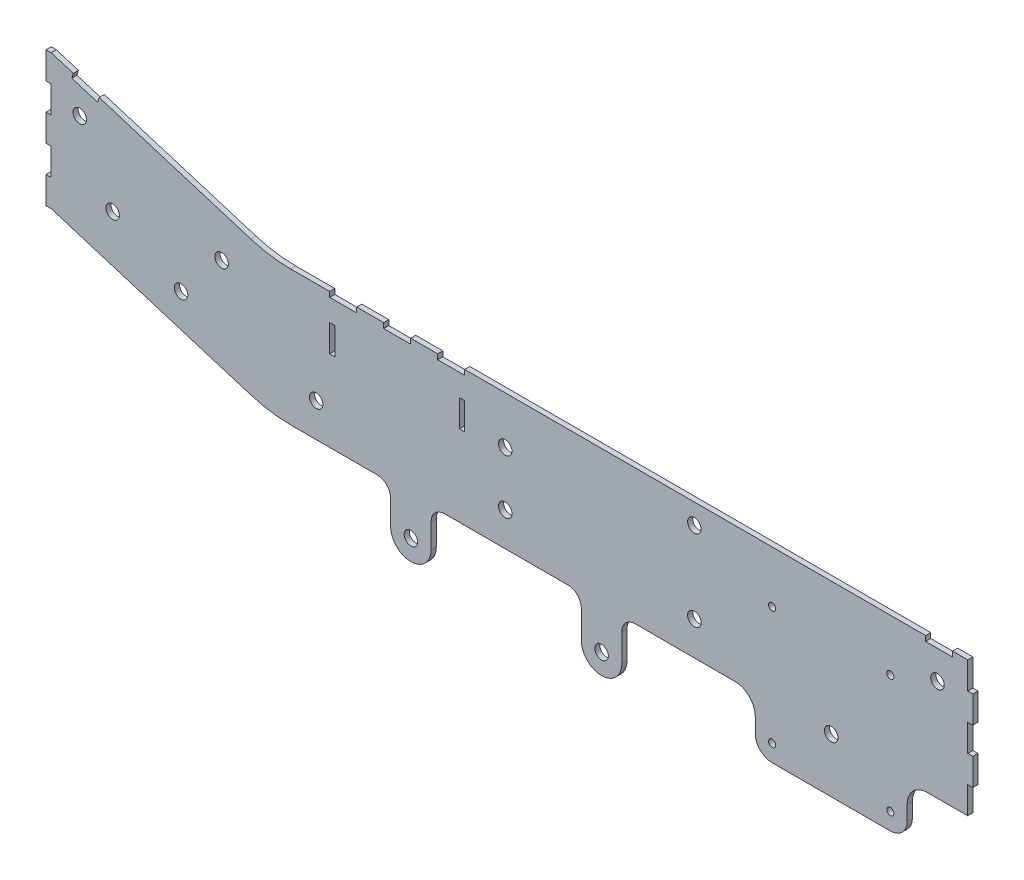
SolidWorks part; units mm, degrees
material "1060 Alloy"
ref_plane "Front Plane" through (0, 0, 0) normal (0, 0, 1) x (1, 0, 0)
ref_plane "Top Plane" through (0, 0, 0) normal (0, 1, 0) x (1, 0, 0)
ref_plane "Right Plane" through (0, 0, 0) normal (1, 0, 0) x (0, 0, -1)
sketch "Sketch2" plane through (0, 0, 0) normal (0, 0, 1) x (1, 0, 0)
  line L41 (-214.6997, -160.1998) -> (-26.8739, -218.0697)
  line L42 (10.5206, -223.6998) -> (91.8093, -223.6998)
  line L43 (104.5093, -236.3998) -> (104.5093, -259.4448)
  line L44 (142.6093, -259.4448) -> (142.6093, -236.3998)
  line L45 (155.3093, -223.6998) -> (271.0993, -223.6998)
  line L46 (283.7993, -236.3998) -> (283.7993, -262.6248)
  line L47 (321.8993, -262.6248) -> (321.8993, -236.3998)
  line L48 (334.5993, -223.6998) -> (476.2017, -223.6998)
  line L49 (561.2969, -223.6998) -> (656.7743, -223.6998)
  line L50 (656.7743, -223.6998) -> (656.7743, -198.2998)
  line L51 (656.7743, -198.2998) -> (651.9483, -198.2998)
  line L52 (651.9483, -198.2998) -> (651.9483, -172.8998)
  line L53 (651.9483, -172.8998) -> (656.7743, -172.8998)
  line L54 (656.7743, -172.8998) -> (656.7743, -147.4998)
  line L55 (656.7743, -147.4998) -> (651.9483, -147.4998)
  line L56 (651.9483, -147.4998) -> (651.9483, -122.0998)
  line L57 (651.9483, -122.0998) -> (656.7743, -122.0998)
  line L58 (656.7743, -122.0998) -> (656.7743, -96.6998)
  line L59 (656.7743, -96.6998) -> (174.1743, -96.6998)
  line L60 (174.1743, -96.6998) -> (174.1743, -101.5258)
  line L61 (174.1743, -101.5258) -> (148.7743, -101.5258)
  line L62 (148.7743, -101.5258) -> (148.7743, -96.6998)
  line L63 (148.7743, -96.6998) -> (123.3743, -96.6998)
  line L64 (123.3743, -96.6998) -> (123.3743, -101.5258)
  line L65 (123.3743, -101.5258) -> (97.9743, -101.5258)
  line L66 (97.9743, -101.5258) -> (97.9743, -96.6998)
  line L67 (97.9743, -96.6998) -> (72.5743, -96.6998)
  line L68 (72.5743, -96.6998) -> (72.5743, -101.5258)
  line L69 (72.5743, -101.5258) -> (47.1743, -101.5258)
  line L70 (47.1743, -101.5258) -> (47.1743, -96.6998)
  line L71 (47.1743, -96.6998) -> (10.5206, -96.6998)
  line L72 (-214.6997, -160.1998) -> (-26.8739, -218.0697)
  line L73 (-219.5257, -33.1998) -> (-219.5257, -58.5998)
  line L74 (-219.5257, -58.5998) -> (-214.6997, -58.5998)
  line L75 (-214.6997, -58.5998) -> (-214.6997, -83.9998)
  line L76 (-214.6997, -83.9998) -> (-219.5257, -83.9998)
  line L77 (-219.5257, -83.9998) -> (-219.5257, -109.3998)
  line L78 (-219.5257, -109.3998) -> (-214.6997, -109.3998)
  line L79 (-214.6997, -109.3998) -> (-214.6997, -134.7998)
  line L80 (-214.6997, -134.7998) -> (-219.5257, -134.7998)
  line L81 (-219.5257, -134.7998) -> (-219.5257, -160.1998)
  line L82 (-26.8739, -91.0697) -> (-169.5568, -47.1085)
  line L83 (10.5206, -223.6998) -> (91.8093, -223.6998)
  line L84 (104.5093, -236.3998) -> (104.5093, -259.4448)
  line L85 (142.6093, -259.4448) -> (142.6093, -236.3998)
  line L86 (155.3093, -223.6998) -> (271.0993, -223.6998)
  line L87 (283.7993, -236.3998) -> (283.7993, -262.6248)
  line L88 (321.8993, -262.6248) -> (321.8993, -236.3998)
  line L89 (334.5993, -223.6998) -> (476.2017, -223.6998)
  line L90 (561.2969, -223.6998) -> (656.7743, -223.6998)
  line L91 (656.7743, -223.6998) -> (656.7743, -198.2998)
  line L92 (656.7743, -198.2998) -> (651.9483, -198.2998)
  line L93 (651.9483, -198.2998) -> (651.9483, -172.8998)
  line L94 (651.9483, -172.8998) -> (656.7743, -172.8998)
  line L95 (656.7743, -172.8998) -> (656.7743, -147.4998)
  line L96 (656.7743, -147.4998) -> (651.9483, -147.4998)
  line L97 (651.9483, -147.4998) -> (651.9483, -122.0998)
  line L98 (651.9483, -122.0998) -> (656.7743, -122.0998)
  line L99 (656.7743, -122.0998) -> (656.7743, -96.6998)
  line L100 (656.7743, -96.6998) -> (174.1743, -96.6998)
  line L101 (174.1743, -96.6998) -> (174.1743, -101.5258)
  line L102 (174.1743, -101.5258) -> (148.7743, -101.5258)
  line L103 (148.7743, -101.5258) -> (148.7743, -96.6998)
  line L104 (148.7743, -96.6998) -> (123.3743, -96.6998)
  line L105 (123.3743, -96.6998) -> (123.3743, -101.5258)
  line L106 (123.3743, -101.5258) -> (97.9743, -101.5258)
  line L107 (97.9743, -101.5258) -> (97.9743, -96.6998)
  line L108 (97.9743, -96.6998) -> (72.5743, -96.6998)
  line L109 (72.5743, -96.6998) -> (72.5743, -101.5258)
  line L110 (72.5743, -101.5258) -> (47.1743, -101.5258)
  line L111 (47.1743, -101.5258) -> (47.1743, -96.6998)
  line L112 (47.1743, -96.6998) -> (10.5206, -96.6998)
  line L113 (-26.8739, -91.0697) -> (-169.5568, -47.1085)
  line L114 (-219.5257, -33.1998) -> (-219.5257, -58.5998)
  line L115 (-219.5257, -58.5998) -> (-214.6997, -58.5998)
  line L116 (-214.6997, -58.5998) -> (-214.6997, -83.9998)
  line L117 (-214.6997, -83.9998) -> (-219.5257, -83.9998)
  line L118 (-219.5257, -83.9998) -> (-219.5257, -109.3998)
  line L119 (-219.5257, -109.3998) -> (-214.6997, -109.3998)
  line L120 (-214.6997, -109.3998) -> (-214.6997, -134.7998)
  line L121 (-214.6997, -134.7998) -> (-219.5257, -134.7998)
  line L122 (-219.5257, -134.7998) -> (-219.5257, -160.1998)
  line L176 (-195.2517, -44.2417) -> (-193.8307, -39.6296)
  line L177 (-195.2517, -44.2417) -> (-193.8307, -39.6296)
  line L178 (-193.8307, -39.6296) -> (-214.6997, -33.1998)
  line L179 (-193.8307, -39.6296) -> (-214.6997, -33.1998)
  line L180 (-169.5568, -47.1085) -> (-170.9777, -51.7206)
  line L181 (-169.5568, -47.1085) -> (-170.9777, -51.7206)
  line L182 (-170.9777, -51.7206) -> (-195.2517, -44.2417)
  line L183 (-170.9777, -51.7206) -> (-195.2517, -44.2417)
  line L412 (-214.6997, -33.1998) -> (-219.5257, -33.1998)
  line L413 (-214.6997, -33.1998) -> (-219.5257, -33.1998)
  line L414 (-219.5257, -160.1998) -> (-214.6997, -160.1998)
  line L415 (-219.5257, -160.1998) -> (-214.6997, -160.1998)
  arc A11 (-26.8739, -218.0697) -> (10.5206, -223.6998) centre (10.5206, -96.6998) ccw
  arc A12 (104.5093, -236.3998) -> (91.8093, -223.6998) centre (91.8093, -236.3998) ccw
  arc A13 (104.5093, -259.4448) -> (142.6093, -259.4448) centre (123.5593, -259.4448) ccw
  arc A14 (155.3093, -223.6998) -> (142.6093, -236.3998) centre (155.3093, -236.3998) ccw
  arc A15 (283.7993, -236.3998) -> (271.0993, -223.6998) centre (271.0993, -236.3998) ccw
  arc A16 (283.7993, -262.6248) -> (321.8993, -262.6248) centre (302.8493, -262.6248) ccw
  arc A17 (334.5993, -223.6998) -> (321.8993, -236.3998) centre (334.5993, -236.3998) ccw
  arc A18 (486.8386, -229.461) -> (476.2017, -223.6998) centre (476.2017, -236.3998) ccw
  arc A19 (486.8386, -229.461) -> (550.66, -229.461) centre (518.7493, -208.6448) ccw
  arc A20 (561.2969, -223.6998) -> (550.66, -229.461) centre (561.2969, -236.3998) ccw
  arc A21 (-26.8739, -218.0697) -> (10.5206, -223.6998) centre (10.5206, -96.6998) ccw
  arc A22 (-26.8739, -91.0697) -> (10.5206, -96.6998) centre (10.5206, 30.3002) ccw
  arc A23 (104.5093, -236.3998) -> (91.8093, -223.6998) centre (91.8093, -236.3998) ccw
  arc A24 (104.5093, -259.4448) -> (142.6093, -259.4448) centre (123.5593, -259.4448) ccw
  arc A25 (155.3093, -223.6998) -> (142.6093, -236.3998) centre (155.3093, -236.3998) ccw
  arc A26 (283.7993, -236.3998) -> (271.0993, -223.6998) centre (271.0993, -236.3998) ccw
  arc A27 (283.7993, -262.6248) -> (321.8993, -262.6248) centre (302.8493, -262.6248) ccw
  arc A28 (334.5993, -223.6998) -> (321.8993, -236.3998) centre (334.5993, -236.3998) ccw
  arc A29 (486.8386, -229.461) -> (476.2017, -223.6998) centre (476.2017, -236.3998) ccw
  arc A30 (486.8386, -229.461) -> (550.66, -229.461) centre (518.7493, -208.6448) ccw
  arc A31 (561.2969, -223.6998) -> (550.66, -229.461) centre (561.2969, -236.3998) ccw
  arc A32 (-26.8739, -91.0697) -> (10.5206, -96.6998) centre (10.5206, 30.3002) ccw
  circle A56 centre (390.0743, -191.9498) radius 6.35
  circle A57 centre (390.0743, -191.9498) radius 6.35
  circle A58 centre (390.0743, -115.7498) radius 6.35
  circle A59 centre (390.0743, -115.7498) radius 6.35
  circle A60 centre (518.7493, -221.3448) radius 6.35
  circle A61 centre (518.7493, -221.3448) radius 6.35
  circle A62 centre (618.6743, -128.4498) radius 6.35
  circle A63 centre (618.6743, -128.4498) radius 6.35
  circle A64 centre (302.8493, -262.6248) radius 6.35
  circle A65 centre (302.8493, -262.6248) radius 6.35
  circle A66 centre (212.2743, -191.9498) radius 6.35
  circle A67 centre (212.2743, -191.9498) radius 6.35
  circle A68 centre (212.2743, -141.1498) radius 6.35
  circle A69 centre (212.2743, -141.1498) radius 6.35
  circle A70 centre (123.5593, -259.4448) radius 6.35
  circle A71 centre (123.5593, -259.4448) radius 6.35
  circle A72 centre (34.4743, -191.9498) radius 6.35
  circle A73 centre (34.4743, -191.9498) radius 6.35
  circle A74 centre (-92.5257, -166.5498) radius 6.35
  circle A75 centre (-92.5257, -166.5498) radius 6.35
  circle A76 centre (-156.8507, -133.7248) radius 6.35
  circle A77 centre (-156.8507, -133.7248) radius 6.35
  circle A78 centre (-54.4257, -122.0998) radius 6.35
  circle A79 centre (-54.4257, -122.0998) radius 6.35
  circle A80 centre (-187.7757, -71.2998) radius 6.35
  circle A81 centre (-187.7757, -71.2998) radius 6.35
  dimension "D1" = 0
  dimension "D2" = 0
  dimension "D3" = 0
  dimension "D4" = 0
  dimension "D5" = 0
  dimension "D6" = 0
  dimension "D7" = 0
  dimension "D8" = 0
  dimension "D9" = 0
  dimension "D10" = 0
  dimension "D11" = 0
  dimension "D12" = 0
  dimension "D13" = 0
  dimension "D14" = 0
extrude "base" add sketch "Sketch2" along normal blind 4.826
sketch "Sketch3" plane through (0, 0, 4.826) normal (0, 0, 1) x (1, 0, 0)
  line L0 (47.1743, -101.5258) -> (47.1743, -96.6998) construction
  line L1 (169.3483, -122.0998) -> (174.1743, -122.0998)
  line L2 (169.3483, -122.0998) -> (169.3483, -147.4998)
  line L3 (169.3483, -147.4998) -> (174.1743, -147.4998)
  line L4 (174.1743, -122.0998) -> (174.1743, -147.4998)
  line L5 (47.1743, -122.0998) -> (52.0003, -122.0998)
  line L6 (47.1743, -122.0998) -> (47.1743, -147.4998)
  line L7 (47.1743, -147.4998) -> (52.0003, -147.4998)
  line L8 (52.0003, -122.0998) -> (52.0003, -147.4998)
  line L9 (174.1743, -96.6998) -> (174.1743, -101.5258) construction
  line L10 (97.9743, -96.6998) -> (72.5743, -96.6998) construction
  dimension "D1" = 4.826
  dimension "D2" = 25.4
  dimension "D3" = 25.4
extrude "center support vertical holes" cut sketch "Sketch3" against normal through all
sketch "Sketch4" plane through (656.7743, 0, 0) normal (1, 0, 0) x (0, 0, -1)
  line L0 (0, -122.0998) -> (0, -96.6998) construction
  line L1 (0, -96.6998) -> (-4.826, -96.6998) construction
  line L2 (-4.826, -96.6998) -> (-4.826, -122.0998) construction
  line L3 (-4.826, -122.0998) -> (0, -122.0998) construction
  line L4 (0, -172.8998) -> (0, -147.4998) construction
  line L5 (0, -147.4998) -> (-4.826, -147.4998) construction
  line L6 (-4.826, -147.4998) -> (-4.826, -172.8998) construction
  line L7 (-4.826, -172.8998) -> (0, -172.8998) construction
  line L8 (0, -223.6998) -> (0, -198.2998) construction
  line L9 (0, -198.2998) -> (-4.826, -198.2998) construction
  line L10 (-4.826, -198.2998) -> (-4.826, -223.6998) construction
  line L11 (-4.826, -223.6998) -> (0, -223.6998) construction
  line L12 (0, -122.0998) -> (0, -96.6998)
  line L13 (0, -96.6998) -> (-4.826, -96.6998)
  line L14 (-4.826, -96.6998) -> (-4.826, -122.0998)
  line L15 (-4.826, -122.0998) -> (0, -122.0998)
  line L16 (0, -172.8998) -> (0, -147.4998)
  line L17 (0, -147.4998) -> (-4.826, -147.4998)
  line L18 (-4.826, -147.4998) -> (-4.826, -172.8998)
  line L19 (-4.826, -172.8998) -> (0, -172.8998)
  line L20 (0, -223.6998) -> (0, -198.2998)
  line L21 (0, -198.2998) -> (-4.826, -198.2998)
  line L22 (-4.826, -198.2998) -> (-4.826, -223.6998)
  line L23 (-4.826, -223.6998) -> (0, -223.6998)
extrude "Cut-Extrude2" cut sketch "Sketch4" against normal blind 9.652
sketch "Sketch5" plane through (0, 0, 0) normal (0, 0, 1) x (1, 0, 0)
  line L0 (463.2122, -272.4369) -> (574.3372, -272.4369)
  line L1 (447.3372, -256.5619) -> (447.3372, -242.7498)
  line L3 (590.2122, -256.5619) -> (590.2122, -242.7498)
  line L43 (647.1223, -198.2998) -> (651.9483, -198.2998)
  line L44 (651.9483, -198.2998) -> (651.9483, -172.8998)
  line L45 (651.9483, -172.8998) -> (647.1223, -172.8998)
  line L46 (647.1223, -172.8998) -> (647.1223, -147.4998)
  line L47 (647.1223, -147.4998) -> (651.9483, -147.4998)
  line L48 (651.9483, -147.4998) -> (651.9483, -122.0998)
  line L49 (651.9483, -122.0998) -> (647.1223, -122.0998)
  line L50 (647.1223, -122.0998) -> (647.1223, -96.6998)
  line L51 (647.1223, -96.6998) -> (174.1743, -96.6998)
  line L52 (174.1743, -96.6998) -> (174.1743, -101.5258)
  line L53 (174.1743, -101.5258) -> (148.7743, -101.5258)
  line L54 (148.7743, -101.5258) -> (148.7743, -96.6998)
  line L55 (148.7743, -96.6998) -> (123.3743, -96.6998)
  line L56 (123.3743, -96.6998) -> (123.3743, -101.5258)
  line L57 (123.3743, -101.5258) -> (97.9743, -101.5258)
  line L58 (97.9743, -101.5258) -> (97.9743, -96.6998)
  line L59 (97.9743, -96.6998) -> (72.5743, -96.6998)
  line L60 (72.5743, -96.6998) -> (72.5743, -101.5258)
  line L61 (72.5743, -101.5258) -> (47.1743, -101.5258)
  line L62 (47.1743, -101.5258) -> (47.1743, -96.6998)
  line L63 (47.1743, -96.6998) -> (10.5206, -96.6998)
  line L64 (-26.8739, -91.0697) -> (-169.5568, -47.1085)
  line L65 (-214.6997, -33.1998) -> (-219.5257, -33.1998)
  line L66 (-219.5257, -33.1998) -> (-219.5257, -58.5998)
  line L67 (-219.5257, -58.5998) -> (-214.6997, -58.5998)
  line L68 (-214.6997, -58.5998) -> (-214.6997, -83.9998)
  line L69 (-214.6997, -83.9998) -> (-219.5257, -83.9998)
  line L70 (-219.5257, -83.9998) -> (-219.5257, -109.3998)
  line L71 (-219.5257, -109.3998) -> (-214.6997, -109.3998)
  line L72 (-214.6997, -109.3998) -> (-214.6997, -134.7998)
  line L73 (-214.6997, -134.7998) -> (-219.5257, -134.7998)
  line L74 (-219.5257, -134.7998) -> (-219.5257, -160.1998)
  line L75 (-219.5257, -160.1998) -> (-214.6997, -160.1998)
  line L76 (-214.6997, -160.1998) -> (-26.8739, -218.0697)
  line L77 (10.5206, -223.6998) -> (91.8093, -223.6998)
  line L78 (104.5093, -236.3998) -> (104.5093, -259.4448)
  line L79 (142.6093, -259.4448) -> (142.6093, -236.3998)
  line L80 (155.3093, -223.6998) -> (271.0993, -223.6998)
  line L81 (283.7993, -236.3998) -> (283.7993, -262.6248)
  line L82 (321.8993, -262.6248) -> (321.8993, -236.3998)
  line L83 (334.5993, -223.6998) -> (476.2017, -223.6998)
  line L84 (561.2969, -223.6998) -> (647.1223, -223.6998)
  line L85 (647.1223, -223.6998) -> (647.1223, -198.2998)
  line L86 (647.1223, -198.2998) -> (651.9483, -198.2998)
  line L87 (651.9483, -198.2998) -> (651.9483, -172.8998)
  line L88 (651.9483, -172.8998) -> (647.1223, -172.8998)
  line L89 (647.1223, -172.8998) -> (647.1223, -147.4998)
  line L90 (647.1223, -147.4998) -> (651.9483, -147.4998)
  line L91 (651.9483, -147.4998) -> (651.9483, -122.0998)
  line L92 (651.9483, -122.0998) -> (647.1223, -122.0998)
  line L93 (647.1223, -122.0998) -> (647.1223, -96.6998)
  line L94 (647.1223, -96.6998) -> (174.1743, -96.6998)
  line L95 (174.1743, -96.6998) -> (174.1743, -101.5258)
  line L96 (174.1743, -101.5258) -> (148.7743, -101.5258)
  line L97 (148.7743, -101.5258) -> (148.7743, -96.6998)
  line L98 (148.7743, -96.6998) -> (123.3743, -96.6998)
  line L99 (123.3743, -96.6998) -> (123.3743, -101.5258)
  line L100 (123.3743, -101.5258) -> (97.9743, -101.5258)
  line L101 (97.9743, -101.5258) -> (97.9743, -96.6998)
  line L102 (97.9743, -96.6998) -> (72.5743, -96.6998)
  line L103 (72.5743, -96.6998) -> (72.5743, -101.5258)
  line L104 (72.5743, -101.5258) -> (47.1743, -101.5258)
  line L105 (47.1743, -101.5258) -> (47.1743, -96.6998)
  line L106 (47.1743, -96.6998) -> (10.5206, -96.6998)
  line L107 (-26.8739, -91.0697) -> (-169.5568, -47.1085)
  line L108 (-214.6997, -33.1998) -> (-219.5257, -33.1998)
  line L109 (-219.5257, -33.1998) -> (-219.5257, -58.5998)
  line L110 (-219.5257, -58.5998) -> (-214.6997, -58.5998)
  line L111 (-214.6997, -58.5998) -> (-214.6997, -83.9998)
  line L112 (-214.6997, -83.9998) -> (-219.5257, -83.9998)
  line L113 (-219.5257, -83.9998) -> (-219.5257, -109.3998)
  line L114 (-219.5257, -109.3998) -> (-214.6997, -109.3998)
  line L115 (-214.6997, -109.3998) -> (-214.6997, -134.7998)
  line L116 (-214.6997, -134.7998) -> (-219.5257, -134.7998)
  line L117 (-219.5257, -134.7998) -> (-219.5257, -160.1998)
  line L118 (-219.5257, -160.1998) -> (-214.6997, -160.1998)
  line L119 (-214.6997, -160.1998) -> (-26.8739, -218.0697)
  line L120 (10.5206, -223.6998) -> (91.8093, -223.6998)
  line L121 (104.5093, -236.3998) -> (104.5093, -259.4448)
  line L122 (142.6093, -259.4448) -> (142.6093, -236.3998)
  line L123 (155.3093, -223.6998) -> (271.0993, -223.6998)
  line L124 (283.7993, -236.3998) -> (283.7993, -262.6248)
  line L125 (321.8993, -262.6248) -> (321.8993, -236.3998)
  line L126 (334.5993, -223.6998) -> (476.2017, -223.6998)
  line L127 (561.2969, -223.6998) -> (647.1223, -223.6998)
  line L128 (647.1223, -223.6998) -> (647.1223, -198.2998)
  line L136 (-169.5568, -47.1085) -> (-170.9777, -51.7206)
  line L137 (-169.5568, -47.1085) -> (-170.9777, -51.7206)
  line L138 (-170.9777, -51.7206) -> (-195.2517, -44.2417)
  line L139 (-170.9777, -51.7206) -> (-195.2517, -44.2417)
  line L140 (-195.2517, -44.2417) -> (-193.8307, -39.6296)
  line L141 (-195.2517, -44.2417) -> (-193.8307, -39.6296)
  line L142 (-193.8307, -39.6296) -> (-214.6997, -33.1998)
  line L143 (-193.8307, -39.6296) -> (-214.6997, -33.1998)
  circle A0 centre (574.3372, -256.5619) radius 3.3528 construction
  circle A1 centre (463.2122, -256.5619) radius 3.3528 construction
  circle A2 centre (463.2122, -145.4369) radius 3.3528 construction
  circle A3 centre (574.3372, -145.4369) radius 3.2512 construction
  circle A4 centre (574.3372, -256.5619) radius 3.3528
  circle A5 centre (463.2122, -256.5619) radius 3.3528
  circle A6 centre (463.2122, -145.4369) radius 3.3528
  circle A7 centre (574.3372, -145.4369) radius 3.2512
  arc A8 (447.3372, -256.5619) -> (463.2122, -272.4369) centre (463.2122, -256.5619) ccw
  arc A9 (574.3372, -272.4369) -> (590.2122, -256.5619) centre (574.3372, -256.5619) ccw
  arc A10 (447.3372, -242.7498) -> (428.2872, -223.6998) centre (428.2872, -242.7498) ccw
  arc A11 (609.2622, -223.6998) -> (590.2122, -242.7498) centre (609.2622, -242.7498) ccw
  arc A21 (-26.8739, -91.0697) -> (10.5206, -96.6998) centre (10.5206, 30.3002) ccw
  arc A22 (-26.8739, -218.0697) -> (10.5206, -223.6998) centre (10.5206, -96.6998) ccw
  arc A23 (104.5093, -236.3998) -> (91.8093, -223.6998) centre (91.8093, -236.3998) ccw
  arc A24 (104.5093, -259.4448) -> (142.6093, -259.4448) centre (123.5593, -259.4448) ccw
  arc A25 (155.3093, -223.6998) -> (142.6093, -236.3998) centre (155.3093, -236.3998) ccw
  arc A26 (283.7993, -236.3998) -> (271.0993, -223.6998) centre (271.0993, -236.3998) ccw
  arc A27 (283.7993, -262.6248) -> (321.8993, -262.6248) centre (302.8493, -262.6248) ccw
  arc A28 (334.5993, -223.6998) -> (321.8993, -236.3998) centre (334.5993, -236.3998) ccw
  arc A29 (486.8386, -229.461) -> (476.2017, -223.6998) centre (476.2017, -236.3998) ccw
  arc A30 (486.8386, -229.461) -> (550.66, -229.461) centre (518.7493, -208.6448) ccw
  arc A31 (561.2969, -223.6998) -> (550.66, -229.461) centre (561.2969, -236.3998) ccw
  arc A32 (-26.8739, -91.0697) -> (10.5206, -96.6998) centre (10.5206, 30.3002) ccw
  arc A33 (-26.8739, -218.0697) -> (10.5206, -223.6998) centre (10.5206, -96.6998) ccw
  arc A34 (104.5093, -236.3998) -> (91.8093, -223.6998) centre (91.8093, -236.3998) ccw
  arc A35 (104.5093, -259.4448) -> (142.6093, -259.4448) centre (123.5593, -259.4448) ccw
  arc A36 (155.3093, -223.6998) -> (142.6093, -236.3998) centre (155.3093, -236.3998) ccw
  arc A37 (283.7993, -236.3998) -> (271.0993, -223.6998) centre (271.0993, -236.3998) ccw
  arc A38 (283.7993, -262.6248) -> (321.8993, -262.6248) centre (302.8493, -262.6248) ccw
  arc A39 (334.5993, -223.6998) -> (321.8993, -236.3998) centre (334.5993, -236.3998) ccw
  arc A40 (486.8386, -229.461) -> (476.2017, -223.6998) centre (476.2017, -236.3998) ccw
  arc A41 (486.8386, -229.461) -> (550.66, -229.461) centre (518.7493, -208.6448) ccw
  arc A42 (561.2969, -223.6998) -> (550.66, -229.461) centre (561.2969, -236.3998) ccw
  arc M56 (455.2747, -263.7056) -> (456.0685, -264.4994) centre (456.0685, -263.7056) ccw
  line M57 (456.0685, -264.4994) -> (581.481, -264.4994)
  arc M58 (581.481, -264.4994) -> (582.2747, -263.7056) centre (581.481, -263.7056) ccw
  line M59 (582.2747, -263.7056) -> (582.2747, -138.2931)
  line M63 (455.2747, -138.2931) -> (455.2747, -263.7056)
  circle M64 centre (480.5665, -220.0494) radius 5.5626
  circle M68 centre (463.2122, -256.5619) radius 3.3528
  circle M70 centre (574.3372, -256.5619) radius 3.3528
  circle M74 centre (556.9829, -220.0494) radius 5.5626
  dimension "D2" = 31.75
  dimension "D3" = 19.05
  dimension "D1" = 0
extrude "Boss-Extrude1" add sketch "Sketch5" along normal through all contours A11 L127 L126 A10 L1 A8 L0 A9 L3 M59 M58 M57 M56 M63 | L127 A42 A41 A40 L126 M74 M64 M63 M56 M57 M58 M59 M70 M68 | A40 M64 | A42 M74
sketch "Sketch6" plane through (0, 0, 4.826) normal (0, 0, 1) x (1, 0, 0)
  circle A0 centre (463.1868, -145.4369) radius 3.3528 construction
  circle A2 centre (463.1868, -145.4369) radius 3.3528
  circle A3 centre (574.3118, -145.4369) radius 3.3528 construction
  circle A4 centre (574.3118, -145.4369) radius 3.3528
extrude "Cut-Extrude3" cut sketch "Sketch6" against normal through all
sketch "Sketch7" plane through (0, -96.6998, 0) normal (0, 1, 0) x (1, 0, 0)
  line L0 (647.1223, -4.826) -> (174.1743, -4.826) construction
  line L1 (632.8983, -4.826) -> (607.4983, -4.826)
  line L2 (632.8983, -4.826) -> (632.8983, 0)
  line L3 (632.8983, 0) -> (607.4983, 0)
  line L4 (607.4983, -4.826) -> (607.4983, 0)
  line L5 (647.1223, 0) -> (174.1743, 0) construction
  line L6 (651.9483, -4.826) -> (651.9483, 0) construction
  dimension "D1" = 25.4
  dimension "D2" = 19.05
extrude "Cut-Extrude4" cut sketch "Sketch7" against normal blind 4.826
equation "\"sheet width\"= .19"
equation "\"width\"= 24.5"
equation "\"length\"= 34.5"
equation "\"standoff hole size\"= .5"
equation "\"ground clearence\"= 3"
equation "\"small drive pulley\"= 74.55mm"
equation "\"large drive pulley\"= 150.95mm"
equation "\"drive axle hole size\"= .5"
equation "\"front pulley clearence\"= 1"
equation "\"center support location\"= 19"
equation "\"D1@Sketch3\"=\"sheet width\""
equation "\"D1@base\"=\"sheet width\""
equation "\"D1@Cut-Extrude2\"=\"sheet width\"*2"
equation "\"D1@Cut-Extrude4\"=\"sheet width\""
